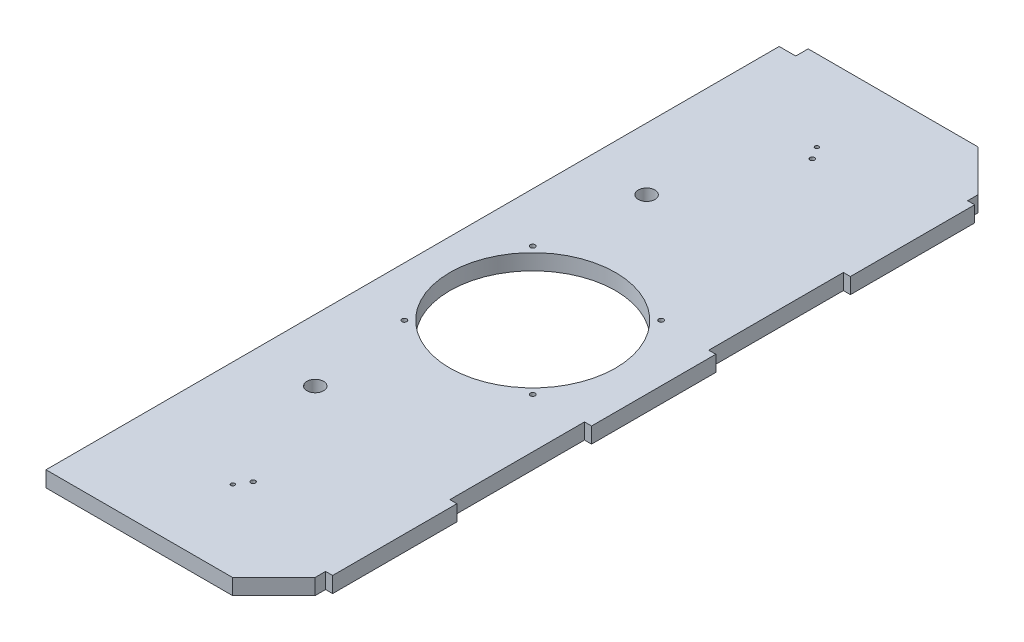
SolidWorks part; units mm, degrees
material "PE High Density"
ref_plane "Front Plane" through (0, 0, 0) normal (0, 0, 1) x (1, 0, 0)
ref_plane "Top Plane" through (0, 0, 0) normal (0, 1, 0) x (1, 0, 0)
ref_plane "Right Plane" through (0, 0, 0) normal (1, 0, 0) x (0, 0, -1)
sketch "Sketch1" plane through (0, 0, 0) normal (0, 1, 0) x (1, 0, 0)
  line L0 (0, 0) -> (0, 457.2)
  line L1 (0, 457.2) -> (139.7, 457.2)
  line L10 (139.7, 457.2) -> (139.7, 0)
  line L11 (139.7, 0) -> (0, 0)
  line L12 (0, 228.6) -> (139.7, 228.6) construction
  circle A0 centre (69.85, 228.6) radius 50.8
  circle A1 centre (38.1, 127) radius 5.08
  circle A3 centre (38.1, 330.2) radius 5.08
  dimension "D11" = 10.16
  dimension "D17" = 10.16
  dimension "D3" = 101.6
  dimension "D2" = 69.85
  dimension "Length of Rib" = 457.2
  dimension "D12" = 127
  dimension "D13" = 38.1
  dimension "D18" = 38.1
  dimension "D19" = 127
  dimension "Width of Rib" = 139.7
extrude "Boss-Extrude1" add sketch "Sketch1" along normal blind 9.652
sketch "Sketch4" plane through (0, 9.652, 0) normal (0, 1, 0) x (1, 0, 0)
  line L10 (0, 457.2) -> (10.16, 457.2)
  line L11 (0, 457.2) -> (0, 449.58)
  line L12 (0, 449.58) -> (10.16, 449.58)
  line L13 (10.16, 457.2) -> (10.16, 449.58)
  dimension "D2" = 7.62
  dimension "D3" = 10.16
extrude "Cut-Extrude1" cut sketch "Sketch4" against normal through all
chamfer "Chamfer1" distance 25.4 angle 45 2 edges at (139.7, 4.826, 0) (139.7, 4.826, -457.2)
sketch "Sketch5" plane through (139.7, 0, 0) normal (1, 0, 0) x (0, 0, -1)
  line L0 (25.4, 9.652) -> (431.8, 9.652) construction
  line L1 (31.75, 9.652) -> (107.95, 9.652)
  line L2 (31.75, 9.652) -> (31.75, 0)
  line L3 (31.75, 0) -> (107.95, 0)
  line L4 (107.95, 9.652) -> (107.95, 0)
  line L5 (25.4, 0) -> (431.8, 0) construction
  line L7 (190.5, 9.652) -> (190.5, 0)
  line L8 (190.5, 9.652) -> (266.7, 9.652)
  line L9 (190.5, 0) -> (266.7, 0)
  line L10 (266.7, 9.652) -> (266.7, 0)
  line L11 (349.25, 9.652) -> (349.25, 0)
  line L12 (349.25, 9.652) -> (425.45, 9.652)
  line L13 (349.25, 0) -> (425.45, 0)
  line L14 (425.45, 9.652) -> (425.45, 0)
  dimension "D2" = 76.2
  dimension "D3" = 3
extrude "Boss-Extrude2" add sketch "Sketch5" along normal blind 4.318
sketch "Sketch7" plane through (0, 9.652, 0) normal (0, 1, 0) x (1, 0, 0)
  line L0 (0, 0) -> (114.3, 0) construction
  line L1 (139.7, 107.95) -> (139.7, 190.5) construction
  line L2 (109.22, 189.23) -> (109.22, 267.97) construction
  line L4 (109.22, 189.23) -> (30.48, 189.23) construction
  line L5 (30.48, 189.23) -> (30.48, 267.97) construction
  line L6 (30.48, 267.97) -> (109.22, 267.97) construction
  point P0 (109.22, 189.23)
  point P2 (30.48, 189.23)
  point P4 (30.48, 267.97)
  point P6 (109.22, 267.97)
  dimension "D1" = 189.23
  dimension "D2" = 30.48
  dimension "D3" = 78.74
  dimension "D4" = 78.74
  dimension "D5" = 78.74
  dimension "D6" = 78.74
hole_wizard "Ø3.0 (3) Diameter Hole1" positions "Sketch7" profile "Sketch8" hole size "Ø3.0" standard "ANSI Metric" end condition up to next
sketch "Sketch8" plane through (109.22, 9.652, -189.23) normal (1, 0, 0) x (0, 0, 1)
  line L0 (0, 0) -> (0, 9.652)
  line L1 (0, 9.652) -> (1.5, 9.652)
  line L2 (1.5, 9.652) -> (1.5, 0)
  line L5 (1.5, 0) -> (0, 0)
  line L11 (0, -6.35) -> (0, 107.95) construction
  dimension "Thru Hole Dia." = 3
  dimension "Thru Hole Depth" = 9.652
sketch "Sketch9" plane through (0, 9.652, 0) normal (0, 1, 0) x (1, 0, 0)
  line L0 (144.018, 228.6) -> (-0.0043, 228.6) construction
  line L1 (144.018, 266.7) -> (144.018, 190.5) construction
ref_plane "Plane1" through (0, 0, -228.6) normal (0, 0, 1) x (1, 0, 0)
ref_plane "Plane2" through (0, 0, -228.6) normal (0, 0, 1) x (1, 0, 0)
sketch "Sketch10" plane through (0, 9.652, 0) normal (0, 1, 0) x (1, 0, 0)
  line L0 (0, 449.58) -> (0, 0) construction
  line L2 (0, 0) -> (114.3, 0) construction
  circle A0 centre (65.024, 49.53) radius 1.1679
  circle A1 centre (69.85, 57.15) radius 1.4162
  dimension "D1" = 65.024
  dimension "D2" = 49.53
  dimension "D3" = 57.15
  dimension "D4" = 69.85
extrude "Cut-Extrude2" cut sketch "Sketch10" against normal up to surface (9.652 mm away) up to face at (109.22, 0, -190.73)
mirror "Mirror1" about plane through (0, 0, -228.6) normal (0, 0, 1) of "Cut-Extrude2"
